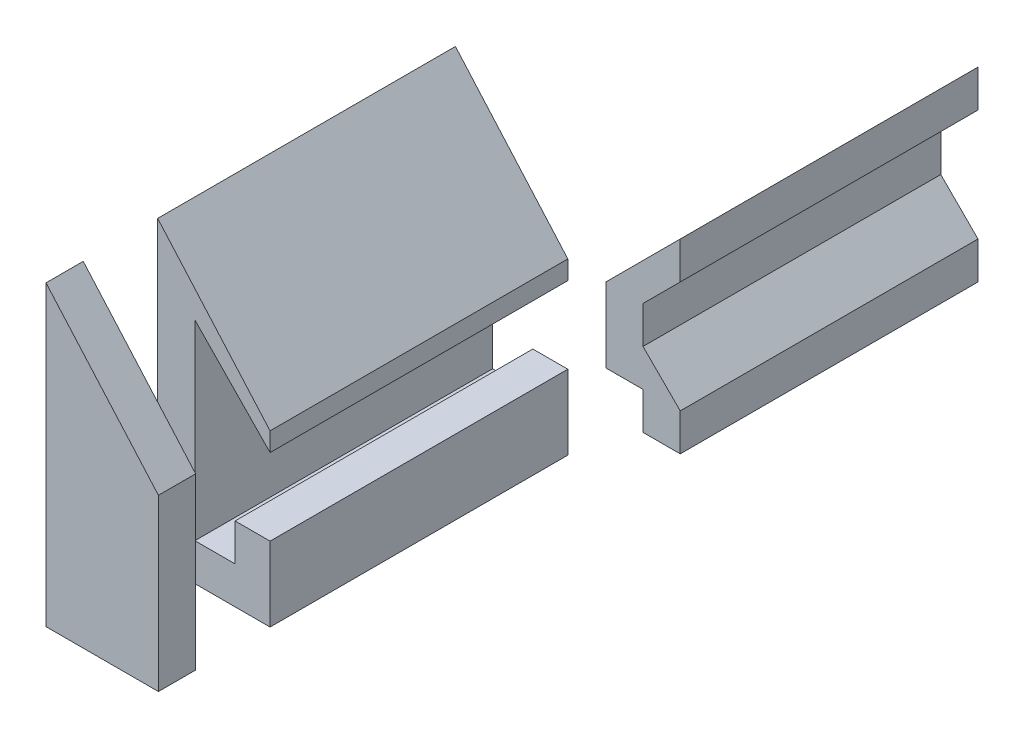
SolidWorks part; units mm, degrees
ref_plane "Front Plane" through (0, 0, 0) normal (0, 0, 1) x (1, 0, 0)
ref_plane "Top Plane" through (0, 0, 0) normal (0, 1, 0) x (1, 0, 0)
ref_plane "Right Plane" through (0, 0, 0) normal (1, 0, 0) x (0, 0, -1)
sketch "Sketch2" plane through (0, 0, 0) normal (0, 0, 1) x (1, 0, 0)
  line L0 (0, 0) -> (0, -20.2389) construction
  line L1 (0, 0) -> (0, 19.4218) construction
  line L2 (0, 10) -> (0, 12.5) construction
  line L3 (-0.1, -10.2) -> (-26.5032, -10.2) construction
  line L4 (-0.1, -0.2) -> (-0.1, -10.2)
  line L5 (-0.1, 12.6319) -> (-15.2, 29.8)
  line L6 (-15.2, 29.8) -> (-15.2, -10.2)
  line L7 (-15.2, -10.2) -> (-0.1, -10.2)
  line L8 (0, 10) -> (-0.1, 10) construction
  line L10 (-0.1, 10.1028) -> (-10.2, 20.4828)
  line L11 (-10.2, 20.4828) -> (-10.2, -5.2)
  line L12 (-10.2, -5.2) -> (-4.8, -5.2)
  line L13 (-4.8, -5.2) -> (-4.8, -0.2)
  line L14 (-4.8, -0.2) -> (-0.1, -0.2)
  line L15 (0, 0) -> (0, -0.6818) construction
  line L17 (-0.1, 10.1028) -> (-0.1, 12.6319)
  dimension "D2" = 0.1
  dimension "D3" = 0.1
  dimension "D4" = 5.4
  dimension "D5" = 25.6828
  dimension "D6" = 40
  dimension "D1" = 2.5
  dimension "D7" = 5
  dimension "D8" = 15.1
  dimension "D9" = 4.7
  dimension "D10" = 5
  dimension "D11" = 0.1
  dimension "D12" = 0.1028
  dimension "D13" = 2.6319
extrude "Boss-Extrude1" add sketch "Sketch2" along normal blind 40
ref_plane "Plane1" through (0, 0, 50) normal (0, 0, 1) x (1, 0, 0)
sketch "Sketch3" plane through (0, 0, 50) normal (0, 0, 1) x (1, 0, 0)
  line L0 (-0.1, -0.2) -> (-0.1, 10.1028)
  line L21 (-0.1, 10.1028) -> (-0.1, 12.6319)
  line L22 (-0.1, 12.6319) -> (-15.2, 29.8)
  line L23 (-15.2, 29.8) -> (-15.2, -10.2)
  line L24 (-15.2, -10.2) -> (-0.1, -10.2)
  line L25 (-0.1, -10.2) -> (-0.1, -0.2)
extrude "Boss-Extrude2" add sketch "Sketch3" along normal blind 5 separate body contours L22 L23 L24 L25 L0 L21
ref_plane "Plane2" through (0, 0, -10) normal (0, 0, -1) x (-1, 0, 0)
sketch "Sketch4" plane through (0, 0, -10) normal (0, 0, -1) x (-1, 0, 0)
  line L0 (5, 2.5) -> (-5, 12.5)
  line L1 (-5, 12.5) -> (-5, 7.5)
  line L2 (0, -12.5) -> (0, -7.5)
  line L3 (0, -7.5) -> (5, -7.5)
  line L4 (-5, -12.5) -> (0, -12.5)
  line L5 (-5, 12.5) -> (-5, 7.5) construction
  line L6 (5, 2.5) -> (0, 2.5) construction
  line L7 (-5, 7.5) -> (0, 2.5)
  line L8 (0, -7.5) -> (0, -2.5) construction
  line L9 (0, 2.5) -> (0, -2.5)
  line L10 (0, -2.5) -> (-5, -7.5)
  line L11 (-5, -7.5) -> (-5, -12.5)
  line L12 (5, 2.5) -> (5, -7.5)
extrude "Boss-Extrude3" add sketch "Sketch4" along normal blind 40 separate body contours L11 L4 L2 L3 L12 L0 L1 L7 L9 L10
